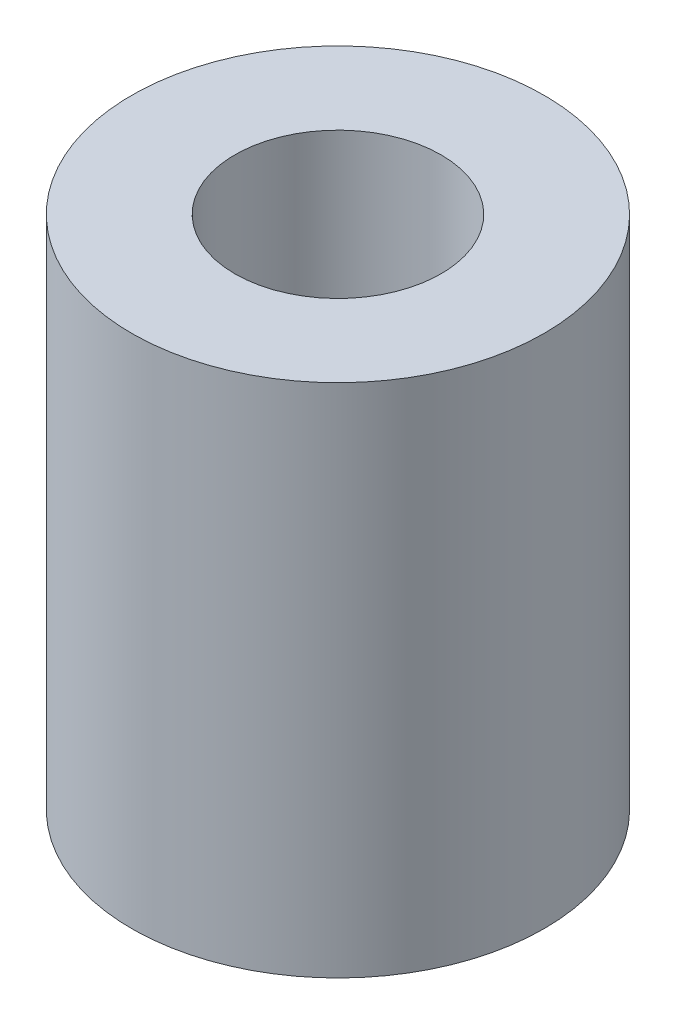
SolidWorks part; units mm, degrees
material "ABS"
ref_plane "Front Plane" through (0, 0, 0) normal (0, 0, 1) x (1, 0, 0)
ref_plane "Top Plane" through (0, 0, 0) normal (0, 1, 0) x (1, 0, 0)
ref_plane "Right Plane" through (0, 0, 0) normal (1, 0, 0) x (0, 0, -1)
sketch "Sketch1" plane through (0, 0, 0) normal (0, 1, 0) x (1, 0, 0)
  circle A0 centre (0, 0) radius 2
  dimension "D1" = 4
extrude "Extrude-Thin1" add sketch "Sketch1" along normal blind 10 thin
